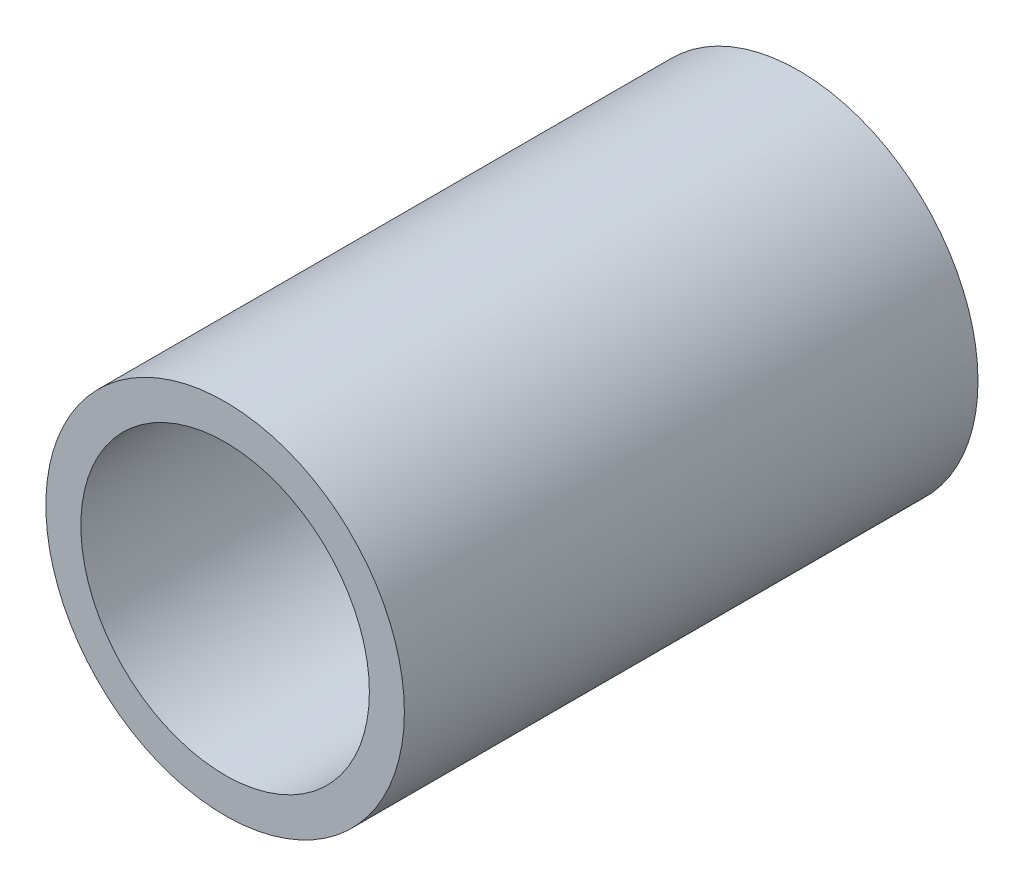
SolidWorks part; units mm, degrees
ref_plane "Front Plane" through (0, 0, 0) normal (0, 0, 1) x (1, 0, 0)
ref_plane "Top Plane" through (0, 0, 0) normal (0, 1, 0) x (1, 0, 0)
ref_plane "Right Plane" through (0, 0, 0) normal (1, 0, 0) x (0, 0, -1)
sketch "Sketch1" plane through (0, 0, 0) normal (0, 0, 1) x (1, 0, 0)
  circle A0 centre (0, 0) radius 7.9375
  circle A1 centre (0, 0) radius 6.3881
  dimension "D1" = 15.875
  dimension "ID" = 12.7762
extrude "Extrude1" add sketch "Sketch1" along normal mid plane 25.4
sketch "Sketch2" plane through (0, 0, 0) normal (1, 0, 0) x (0, 0, -1)
  line L0 (-12.7, -6.3881) -> (12.7, -6.3881) construction
  line L3 (12.7, 6.3881) -> (-12.7, 6.3881) construction
  line L5 (-12.7, -6.3881) -> (12.7, -6.3881)
  line L6 (12.7, 6.3881) -> (-12.7, 6.3881)
sketch "Sketch4" plane through (0, 0, 12.7) normal (0, 0, 1) x (1, 0, 0)
  line L0 (0, 0) -> (-4.5171, 4.5171)
  line L1 (0, -20.955) -> (0, 20.955) construction
  circle A0 centre (0, 0) radius 6.3881 construction
  dimension "D1" = 45
